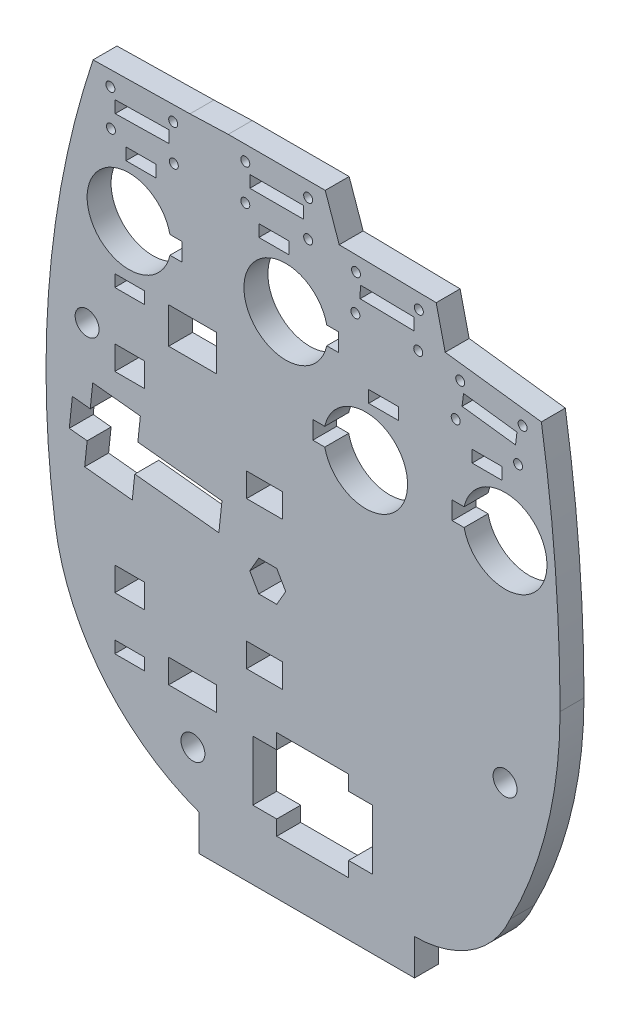
SolidWorks part; units mm, degrees
ref_plane "Front Plane" through (0, 0, 0) normal (0, 0, 1) x (1, 0, 0)
ref_plane "Top Plane" through (0, 0, 0) normal (0, 1, 0) x (1, 0, 0)
ref_plane "Right Plane" through (0, 0, 0) normal (1, 0, 0) x (0, 0, -1)
sketch "Sketch1" plane through (0, 0, 0) normal (0, 0, 1) x (1, 0, 0)
  line L0 (-4.5, 78.51) -> (-4.5, 76.51)
  line L1 (4.5, 78.51) -> (-4.5, 78.51)
  line L2 (-12.9786, -18) -> (-12.9786, -24)
  line L3 (-9.666, 24.0723) -> (-9.153, 28.9531)
  line L4 (-4.5, 76.51) -> (4.5, 76.51)
  line L5 (4.5, 76.51) -> (4.5, 78.51)
  line L6 (-34.6568, 26.6989) -> (-34.1438, 31.5798)
  line L7 (10.3588, 63.1512) -> (10.3588, 60.1512)
  line L8 (-8.1, 82.51) -> (8.1, 82.51)
  line L9 (8.3588, 63.1512) -> (10.3588, 63.1512)
  line L10 (10.4412, 75.8064) -> (26.6388, 75.5236)
  line L11 (32.6473, 57.3216) -> (37.6473, 57.3216)
  line L12 (0, 0) -> (-22.59, 0) construction
  line L13 (10.3588, 60.1512) -> (8.3588, 60.1512)
  line L14 (-17.8416, 63.1512) -> (-15.8416, 63.1512)
  line L15 (-15.8416, 63.1512) -> (-15.8416, 60.1512)
  line L16 (-15.8416, 60.1512) -> (-17.8416, 60.1512)
  line L17 (32.6473, 55.3216) -> (37.6473, 55.3216)
  line L18 (37.6473, 55.3216) -> (37.6473, 57.3216)
  line L19 (32.6473, 57.3216) -> (32.6473, 55.3216)
  line L20 (-27.0195, 78.062) -> (-18.0208, 78.2192)
  line L21 (-27.0195, 78.062) -> (-26.9845, 76.0623)
  line L22 (-10.0543, 52.8756) -> (-18.0543, 52.8756)
  line L23 (-9.153, 28.9531) -> (-23.2041, 30.43)
  line L24 (-26.9845, 76.0623) -> (-17.9858, 76.2195)
  line L25 (-24.1352, 21.571) -> (-32.0914, 22.4072)
  line L26 (-32.0914, 22.4072) -> (-31.6733, 26.3853)
  line L27 (-23.7171, 25.5491) -> (-9.666, 24.0723)
  line L28 (-17.9858, 76.2195) -> (-18.0208, 78.2192)
  line L29 (15.3631, 57.3216) -> (20.3631, 57.3216)
  line L30 (15.3631, 55.3216) -> (20.3631, 55.3216)
  line L31 (-12.9786, -24) -> (23.0214, -24)
  line L32 (20.3631, 55.3216) -> (20.3631, 57.3216)
  line L33 (23.0214, -24) -> (23.0214, -18)
  line L34 (15.3631, 57.3216) -> (15.3631, 55.3216)
  line L35 (-2.9786, 72.1512) -> (2.0214, 72.1512)
  line L36 (13.9709, 71.7441) -> (13.936, 69.7444)
  line L37 (13.936, 69.7444) -> (22.9346, 69.5874)
  line L38 (8.0257, 48.3216) -> (6.0257, 48.3216)
  line L39 (-2.9786, 70.1512) -> (2.0214, 70.1512)
  line L40 (22.9695, 71.5871) -> (13.9709, 71.7441)
  line L41 (6.0257, 48.3216) -> (6.0257, 45.3216)
  line L42 (22.9346, 69.5874) -> (22.9695, 71.5871)
  line L43 (-22.59, 0) -> (-22.59, 82.14) construction
  line L44 (2.0214, 70.1512) -> (2.0214, 72.1512)
  line L45 (18.54, 75.665) -> (18.5934, 78.7251) construction
  line L46 (-2.9786, 72.1512) -> (-2.9786, 70.1512)
  line L47 (40.1436, 63.5476) -> (31.2139, 64.6755)
  line L48 (6.0257, 45.3216) -> (8.0257, 45.3216)
  line L49 (29.3099, 45.3216) -> (31.3099, 45.3216)
  line L50 (29.3099, 48.3216) -> (29.3099, 45.3216)
  line L51 (31.3099, 48.3216) -> (29.3099, 48.3216)
  line L52 (-22.786, 34.408) -> (-30.7422, 35.2443)
  line L53 (31.2139, 64.6755) -> (30.9632, 62.6912)
  line L54 (-25.179, 72.1512) -> (-20.179, 72.1512)
  line L55 (-30.6888, 81.9985) -> (-14.4912, 82.2815)
  line L56 (44.2162, 67.065) -> (28.1438, 69.095)
  line L57 (-25.179, 70.1512) -> (-20.179, 70.1512)
  line L58 (30.9632, 62.6912) -> (39.893, 61.5633)
  line L59 (-20.179, 70.1512) -> (-20.179, 72.1512)
  line L60 (-25.179, 72.1512) -> (-25.179, 70.1512)
  line L61 (39.893, 61.5633) -> (40.1436, 63.5476)
  line L62 (-34.6568, 26.6989) -> (-31.6733, 26.3853)
  line L63 (-4, -2.5) -> (0, -2.5)
  line L64 (12, 0) -> (0, 0)
  line L65 (12, 0) -> (12, -2.5)
  line L66 (12, -15) -> (0, -15)
  line L67 (-30.7422, 35.2443) -> (-31.1603, 31.2662)
  line L68 (-23.2041, 30.43) -> (-22.786, 34.408)
  line L69 (-34.1438, 31.5798) -> (-31.1603, 31.2662)
  line L70 (-24.1352, 21.571) -> (-23.7171, 25.5491)
  line L71 (16, -7.5) -> (38.9913, -7.5) construction
  line L72 (0, -15) -> (0, -12.5)
  line L73 (-4, -12.5) -> (-4, -2.5)
  line L74 (-4, -12.5) -> (0, -12.5)
  line L75 (0, -2.5) -> (0, 0)
  line L76 (0, 0) -> (0, 82.51) construction
  line L77 (-22.0543, 52.8756) -> (-27.0543, 52.8756)
  line L78 (-10.0543, -2.1244) -> (-18.0543, -2.1244)
  line L79 (-22.0543, -2.1244) -> (-27.0543, -2.1244)
  line L80 (0, 0) -> (18.54, 0) construction
  line L81 (16, -12.5) -> (12, -12.5)
  line L82 (16, -12.5) -> (16, -2.5)
  line L83 (16, -2.5) -> (12, -2.5)
  line L84 (12, -12.5) -> (12, -15)
  line L85 (-9.4095, 26.5127) -> (6.8682, 24.8018) construction
  line L86 (0, 23.7547) -> (-3, 23.7547)
  line L87 (-3, 23.7547) -> (-4.5, 21.1566)
  line L88 (-4.5, 21.1566) -> (-3, 18.5585)
  line L89 (18.54, 0) -> (18.54, 75.665) construction
  line L90 (0, 0) -> (36.18, 0) construction
  line L91 (36.18, 0) -> (36.18, 68.08) construction
  line L92 (28.1438, 69.095) -> (26.6388, 75.5236)
  line L93 (10.4412, 75.8064) -> (8.1, 82.51)
  line L94 (-8.1, 82.51) -> (-14.4912, 82.2815)
  line L95 (-34.6568, 26.6989) -> (47.3354, 26.6989) construction
  line L96 (35.6788, 64.1115) -> (36.18, 68.08) construction
  line L97 (-3, 18.5585) -> (0, 18.5585)
  line L98 (0, 18.5585) -> (1.5, 21.1566)
  line L99 (1.5, 21.1566) -> (0, 23.7547)
  line L100 (0, 18.5585) -> (-3, 23.7547) construction
  line L101 (0, 23.7547) -> (-3, 18.5585) construction
  line L102 (38.1473, 11.8216) -> (-37.0527, 11.8216) construction
  line L103 (-27.7956, 79.5486) -> (-30.6451, 79.4989) construction
  line L104 (0.9634, 10.717) -> (0.9634, 6.717)
  line L105 (0.9634, 6.717) -> (-5.0366, 6.717)
  line L106 (-5.0366, 6.717) -> (-5.0366, 10.717)
  line L107 (-5.0366, 10.717) -> (0.9634, 10.717)
  line L108 (-5.0366, 31.3356) -> (0.9634, 31.3356)
  line L109 (-5.0366, 35.3356) -> (-5.0366, 31.3356)
  line L110 (0.9634, 35.3356) -> (-5.0366, 35.3356)
  line L111 (0.9634, 31.3356) -> (0.9634, 35.3356)
  line L112 (-30.6451, 79.4989) -> (-30.6888, 81.9985) construction
  line L113 (-17.2971, 79.732) -> (-14.4475, 79.7819) construction
  line L114 (-14.4475, 79.7819) -> (-14.4912, 82.2815) construction
  line L115 (-22.5201, 78.1406) -> (-22.59, 82.14) construction
  line L116 (5.25, 80.01) -> (8.1, 80.01) construction
  line L117 (8.1, 80.01) -> (8.1, 82.51) construction
  line L118 (-5.25, 80.01) -> (-8.1, 80.01) construction
  line L119 (-22.0543, -0.1244) -> (-27.0543, -0.1244)
  line L120 (-8.1, 80.01) -> (-8.1, 82.51) construction
  line L121 (-10.0543, 1.8756) -> (-10.0543, -2.1244)
  line L122 (30.6581, 66.2576) -> (27.8306, 66.6147) construction
  line L123 (-10.0543, 52.8756) -> (-10.0543, 46.8756)
  line L124 (-10.0543, 1.8756) -> (-18.0543, 1.8756)
  line L125 (-18.0543, 1.8756) -> (-18.0543, -2.1244)
  line L126 (27.8306, 66.6147) -> (28.1438, 69.095) construction
  line L127 (13.2472, 73.257) -> (10.3976, 73.3067) construction
  line L128 (-22.0543, -0.1244) -> (-22.0543, -2.1244)
  line L129 (-27.0543, -0.1244) -> (-27.0543, -2.1244)
  line L130 (30.6581, 66.2576) -> (29.9062, 60.3049) construction
  line L131 (-10.0543, 46.8756) -> (-18.0543, 46.8756)
  line L132 (-27.0543, 52.8756) -> (-27.0543, 50.8756)
  line L133 (-18.0543, 46.8756) -> (-18.0543, 52.8756)
  line L134 (10.4412, 75.8064) -> (10.3976, 73.3067) construction
  line L135 (-22.0543, 6.717) -> (-22.0543, 10.717)
  line L136 (-22.0543, 10.717) -> (-27.0543, 10.717)
  line L137 (-27.0543, 50.8756) -> (-22.0543, 50.8756)
  line L138 (-22.0543, 52.8756) -> (-22.0543, 50.8756)
  line L139 (-27.0543, 10.717) -> (-27.0543, 6.717)
  line L140 (-27.0543, 6.717) -> (-22.0543, 6.717)
  line L141 (-27.0543, 38.7272) -> (-22.0543, 38.7272)
  line L142 (-22.0543, 38.7272) -> (-22.0543, 42.7272)
  line L143 (-22.0543, 42.7272) -> (-27.0543, 42.7272)
  line L144 (-27.0543, 42.7272) -> (-27.0543, 38.7272)
  line L145 (23.7456, 73.0738) -> (26.5951, 73.024) construction
  line L146 (26.5951, 73.024) -> (26.6388, 75.5236) construction
  line L147 (41.0753, 64.9418) -> (43.9029, 64.5847) construction
  line L148 (41.0753, 64.9418) -> (40.3235, 58.9891) construction
  line L149 (40.3235, 58.9891) -> (43.151, 58.632) construction
  line L150 (43.151, 58.632) -> (43.9029, 64.5847) construction
  line L151 (23.7456, 73.0738) -> (23.6409, 67.0747) construction
  line L152 (13.2472, 73.257) -> (13.1425, 67.2579) construction
  line L153 (-17.2971, 79.732) -> (-17.1923, 73.733) construction
  line L154 (-27.7956, 79.5486) -> (-27.6908, 73.5496) construction
  line L155 (38.1473, 46.8216) -> (38.1473, 11.8216) construction
  arc A0 (-37.0527, 11.8216) -> (-30.6888, 81.9985) centre (116.3395, 33.2885) cw
  circle A1 centre (-1.5, 21.1566) radius 4.5 construction
  arc A2 (8.3588, 63.1512) -> (8.3588, 60.1512) centre (1.5214, 61.6512) ccw
  arc A3 (8.0257, 45.3216) -> (8.0257, 48.3216) centre (14.8631, 46.8216) ccw
  arc A4 (-17.8416, 63.1512) -> (-17.8416, 60.1512) centre (-24.679, 61.6512) ccw
  arc A5 (31.3099, 45.3216) -> (31.3099, 48.3216) centre (38.1473, 46.8216) ccw
  arc A6 (23.0214, -18) -> (38.9913, -7.5) centre (23.0214, -0.6053) ccw
  arc A7 (47.3354, 26.6989) -> (38.9913, -7.5) centre (-26.9196, 26.6989) cw
  arc A8 (-37.0527, 11.8216) -> (-12.9786, -18) centre (-0.147, 16.9865) ccw
  arc A9 (47.3354, 26.6989) -> (44.2162, 67.065) centre (-215.4084, 26.6989) ccw
  circle A11 centre (38.1473, 11.8216) radius 2
  circle A12 centre (-14, -9.1244) radius 2
  circle A18 centre (-5.25, 80.01) radius 0.75
  circle A22 centre (-31.6815, 43.4564) radius 2
  circle A49 centre (5.25, 80.01) radius 0.75
  circle A50 centre (5.25, 74.01) radius 0.75
  circle A51 centre (-5.25, 74.01) radius 0.75
  circle A52 centre (-27.7956, 79.5486) radius 0.75
  circle A53 centre (-17.2971, 79.732) radius 0.75
  circle A54 centre (-27.6908, 73.5496) radius 0.75
  circle A55 centre (-17.1923, 73.733) radius 0.75
  circle A56 centre (23.6409, 67.0747) radius 0.75
  circle A57 centre (13.1425, 67.2579) radius 0.75
  circle A58 centre (23.7456, 73.0738) radius 0.75
  circle A59 centre (13.2472, 73.257) radius 0.75
  circle A60 centre (29.9062, 60.3049) radius 0.7496
  circle A61 centre (41.0753, 64.9418) radius 0.7496
  circle A62 centre (30.6581, 66.2576) radius 0.7496
  circle A63 centre (40.3235, 58.9891) radius 0.7496
  dimension "D1" = 4
  dimension "D2" = 1.5
  dimension "D11" = 1.5214
  dimension "D12" = 2.0214
  dimension "D16" = 6.0257
  dimension "D17" = 4
  dimension "D18" = 8.3588
  dimension "D19" = 22.59
  dimension "D22" = 4
  dimension "D23" = 18.54
  dimension "D24" = 75.665
  dimension "D25" = 12
  dimension "D35" = 4
  dimension "D36" = 16.2
  dimension "D37" = 2
  dimension "D38" = 29.3099
  dimension "D39" = 2.85
  dimension "D40" = 46.8216
  dimension "D43" = 2.85
  dimension "D44" = 24.679
  dimension "D45" = 9
  dimension "D46" = 0.7292
  dimension "D47" = 4.9078
  dimension "D49" = 5.0366
  dimension "D51" = 9.666
  dimension "D55" = 24
  dimension "D56" = 15.8416
  dimension "D13" = 4
  dimension "D58" = 2.5
  dimension "D59" = 18.0543
  dimension "D60" = 8.1
  dimension "D61" = 6
  dimension "D63" = 22.0543
  dimension "D64" = 2.5
  dimension "D65" = 2.85
  dimension "D52" = 10.0543
  dimension "D48" = 25.1285
  dimension "D53" = 12.9786
  dimension "D57" = 4
  dimension "D69" = 6
  dimension "D70" = 2.5
  dimension "D71" = 1.8756
  dimension "D79" = 43.4564
  dimension "D82" = 55.3216
  dimension "D67" = 2.5
  dimension "D68" = 31.6815
  dimension "D5" = 7
  dimension "D29" = 2.5
  dimension "D83" = 8.1
  dimension "D85" = 2
  dimension "D10" = 0.9634
  dimension "D14" = 82.51
  dimension "D15" = 3
  dimension "D20" = 10
  dimension "D21" = 82.14
  dimension "D26" = 15.3631
  dimension "D27" = 2.5
  dimension "D28" = 0
  dimension "D30" = 20.3631
  dimension "D31" = 36.18
  dimension "D32" = 68.08
  dimension "D33" = 23.0214
  dimension "D34" = 6
  dimension "D41" = 14.8631
  dimension "D42" = 32.6473
  dimension "D50" = 9.153
  dimension "D54" = 14
  dimension "D62" = 20.179
  dimension "D66" = 2.85
  dimension "D72" = 6.717
  dimension "D73" = 9.0001
  dimension "D74" = 9.0007
  dimension "D75" = 35
  dimension "D76" = 21.571
  dimension "D77" = 31.3356
  dimension "D78" = 6
  dimension "D80" = 45.3216
  dimension "D81" = 46.8756
  dimension "D84" = 60.1512
  dimension "D86" = 70.1512
  dimension "D93" = 9.1244
extrude "Boss-Extrude1" add sketch "Sketch1" along normal blind 4
equation "\"D14@Sketch1\"= \"HL@parametersSketch@prostheticParameters.SLDPRT\" * 0.446'Mioddle Base Frame "
equation "\"D19@Sketch1\"= \"HB@parametersSketch@prostheticParameters.SLDPRT\" * 0.251'Index Base Frame X"
equation "\"D21@Sketch1\"= \"HL@parametersSketch@prostheticParameters.SLDPRT\" * 0.444'Index Base Frame Y"
equation "\"D23@Sketch1\"= \"HB@parametersSketch@prostheticParameters.SLDPRT\" * 0.206'Ring Base Frame X"
equation "\"D24@Sketch1\"= \"HL@parametersSketch@prostheticParameters.SLDPRT\" * 0.409'Ring Base Frame Y"
equation "\"D31@Sketch1\"= \"HB@parametersSketch@prostheticParameters.SLDPRT\" * 0.402'Pinky Base Frame X"
equation "\"D32@Sketch1\"= \"HL@parametersSketch@prostheticParameters.SLDPRT\" * 0.368'Pinky Base Frame Y"
equation "\"D36@Sketch1\"= \"fingerWidth@parametersSketch@prostheticParameters.SLDPRT\"'Fingers Width"
equation "\"D76@Sketch1\"= \"HL@parametersSketch@prostheticParameters.SLDPRT\" * 0.1166'Hole Thumb Y"
equation "\"D51@Sketch1\"= \"HB@parametersSketch@prostheticParameters.SLDPRT\" * 0.1074'Hole Thumb X1"
equation "\"D50@Sketch1\" = \"HB@parametersSketch@prostheticParameters.SLDPRT\" * 0.1017'Hole Thumb X2"
equation "\"D73@Sketch1\"= \"fingerWidth@parametersSketch@prostheticParameters.SLDPRT\" * 0.55556"
equation "\"D74@Sketch1\"= \"fingerWidth@parametersSketch@prostheticParameters.SLDPRT\" * 0.5556"
equation "\"D60@Sketch1\"= \"fingerWidth@parametersSketch@prostheticParameters.SLDPRT\" / 2"
equation "\"D83@Sketch1\"= \"fingerWidth@parametersSketch@prostheticParameters.SLDPRT\" / 2"
